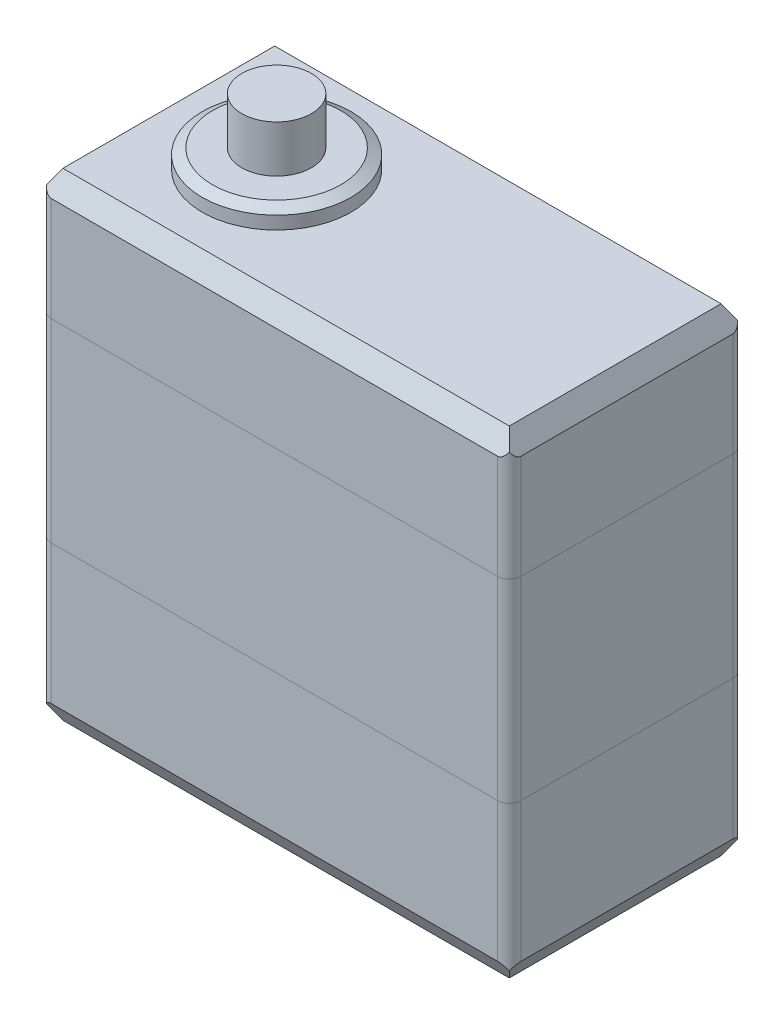
SolidWorks part; units mm, degrees
ref_plane "Front Plane" through (0, 0, 0) normal (0, 0, 1) x (1, 0, 0)
ref_plane "Top Plane" through (0, 0, 0) normal (0, 1, 0) x (1, 0, 0)
ref_plane "Right Plane" through (0, 0, 0) normal (1, 0, 0) x (0, 0, -1)
sketch "Sketch1" plane through (0, 0, 0) normal (0, 1, 0) x (1, 0, 0)
  line L1 (0, 0) -> (40.05, 0)
  line L2 (0, 0) -> (0, 20.05)
  line L3 (0, 20.05) -> (40.05, 20.05)
  line L4 (40.05, 0) -> (40.05, 20.05)
  dimension "D1" = 20.05
  dimension "D2" = 40.05
extrude "Boss-Extrude1" add sketch "Sketch1" along normal blind 40.75
sketch "Sketch2" plane through (0, 40.75, 0) normal (0, 1, 0) x (1, 0, 0)
  line L0 (0, 10.025) -> (40.05, 10.025) construction
  line L1 (0, 20.05) -> (0, 0) construction
  line L2 (40.05, 0) -> (40.05, 20.05) construction
  circle A0 centre (10.19, 10.025) radius 6.34
  dimension "D1" = 29.86
  dimension "D2" = 12.68
extrude "Boss-Extrude2" add sketch "Sketch2" along normal blind 1.6
sketch "Sketch3" plane through (0, 42.35, 0) normal (0, 1, 0) x (1, 0, 0)
  circle A0 centre (10.19, 10.025) radius 2.97
  dimension "D1" = 5.94
extrude "Boss-Extrude3" add sketch "Sketch3" along normal blind 4
ref_plane "Plane1" through (0, 20.375, 0) normal (0, 1, 0) x (1, 0, 0)
mirror "Mirror1" about plane through (0, 20.375, 0) normal (0, 1, 0) of "Boss-Extrude2"
sketch "Sketch4" plane through (0, -1.6, 0) normal (0, -1, 0) x (1, 0, 0)
  circle A0 centre (10.19, -10.025) radius 2.5
  dimension "D1" = 5
extrude "Boss-Extrude4" add sketch "Sketch4" along normal blind 4
sketch "Sketch5" plane through (40.05, 0, 0) normal (1, 0, 0) x (0, 0, -1)
  line L0 (0, 30.15) -> (20.05, 30.15)
  line L1 (0, 40.75) -> (0, 0) construction
  line L2 (20.05, 40.75) -> (20.05, 0) construction
  line L3 (0, 13.6) -> (20.05, 13.6)
  line L4 (0, 40.75) -> (20.05, 40.75) construction
  line L5 (0, 0) -> (20.05, 0) construction
  dimension "D1" = 10.6
  dimension "D2" = 13.6
split "Split1" trim tools "Sketch5" bodies to split 105 resulting bodies 106 107 108
chamfer "Chamfer1" distance 1 angle 60 4 edges at (20.025, 40.75, -20.05) (40.05, 40.75, -10.025) (20.025, 40.75, 0) (0, 40.75, -10.025)
chamfer "Chamfer2" distance 1 angle 60 4 edges at (40.05, 0, -10.025) (20.025, 0, 0) (0, 0, -10.025) (20.025, 0, -20.05)
fillet "Fillet1" radius 1 4 edges at (40.05, 34.584, 0) (40.05, 34.584, -20.05) (0, 34.584, -20.05) (0, 34.584, 0)
fillet "Fillet2" radius 1 4 edges at (0, 21.875, -20.05) (40.05, 21.875, -20.05) (40.05, 21.875, 0) (0, 21.875, 0)
fillet "Fillet3" radius 1 4 edges at (0, 7.666, -20.05) (40.05, 7.666, -20.05) (40.05, 7.666, 0) (0, 7.666, 0)
chamfer "Chamfer3" distance 0.5 angle 60 1 edges at (10.19, 42.35, -3.685)
chamfer "Chamfer4" distance 0.5 angle 60 1 edges at (10.19, -1.6, -3.685)
sketch "Sketch6" plane through (0, 0, 0) normal (-1, 0, 0) x (0, 0, 1)
  line L0 (-10.025, 39.0179) -> (-10.025, 1.7321) construction
  line L1 (-1, 39.0179) -> (-19.05, 39.0179) construction
  line L2 (-19.05, 1.7321) -> (-1, 1.7321) construction
  line L3 (-19.05, 40.75) -> (-1, 40.75) construction
  line L4 (-13.375, 33.45) -> (-6.675, 33.45)
  line L5 (-13.375, 33.45) -> (-13.375, 29.45)
  line L6 (-13.375, 29.45) -> (-6.675, 29.45)
  line L7 (-6.675, 33.45) -> (-6.675, 29.45)
  line L8 (-13.375, 33.45) -> (-6.675, 29.45) construction
  line L9 (-13.375, 29.45) -> (-6.675, 33.45) construction
  point P6 (-10.025, 31.45)
  dimension "D1" = 4
  dimension "D2" = 6.7
  dimension "D3" = 7.3
extrude "Boss-Extrude5" add sketch "Sketch6" along normal blind 5.6
